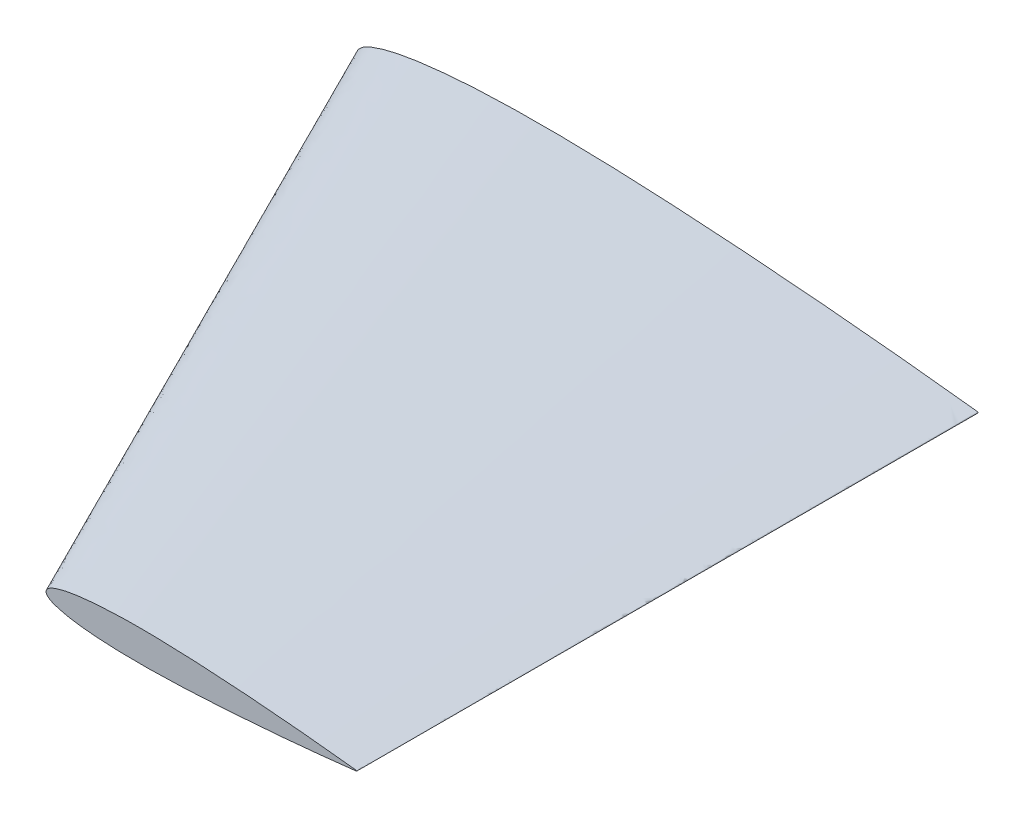
SolidWorks part; units mm, degrees
ref_plane "Front Plane" through (0, 0, 0) normal (0, 0, 1) x (1, 0, 0)
ref_plane "Top Plane" through (0, 0, 0) normal (0, 1, 0) x (1, 0, 0)
ref_plane "Right Plane" through (0, 0, 0) normal (1, 0, 0) x (0, 0, -1)
curve "Curve5"
  spline degree 3 poles (200, 0.21, 0) (196.6671, 0.5908, 0) (190.0035, 1.3521, 0) (176.6737, 2.7751, 0) (160.0099, 4.4044, 0) (140.0096, 6.1482, 0) (120.0099, 7.658, 0) (100.0092, 8.876, 0) (80.0082, 9.7553, 0) (63.3342, 10.0604, 0) (49.9974, 9.9402, 0) (39.9929, 9.6083, 0) (29.9799, 8.984, 0) (21.645, 8.086, 0) (14.9711, 7.038, 0) (9.9602, 5.9907, 0) (5.6938, 4.6887, 0) (2.1576, 3.1984, 0) (-1.278, 0, 0) (2.1576, -3.1984, 0) (5.6938, -4.6887, 0) (9.9602, -5.9907, 0) (14.9711, -7.038, 0) (21.645, -8.086, 0) (29.9799, -8.984, 0) (39.9929, -9.6083, 0) (49.9974, -9.9402, 0) (63.3342, -10.0604, 0) (80.0082, -9.7553, 0) (100.0092, -8.876, 0) (120.0099, -7.658, 0) (140.0096, -6.1482, 0) (160.0099, -4.4044, 0) (176.6737, -2.7751, 0) (190.0035, -1.3521, 0) (196.6671, -0.5908, 0) (200, -0.21, 0) knots 0 0 0 0 0.024822 0.049628 0.099196 0.148713 0.198182 0.247603 0.296978 0.346315 0.370982 0.395662 0.420379 0.445196 0.457685 0.470303 0.483222 0.490061 0.5 0.509939 0.516778 0.529697 0.542315 0.554804 0.579621 0.604338 0.629018 0.653685 0.703022 0.752397 0.801818 0.851287 0.900804 0.950372 0.975178 1 1 1 1
sketch "Sketch7" plane through (0, 0, 0) normal (0, 0, 1) x (1, 0, 0)
  arc A0 (200, 0.21) -> (200, -0.21) centre (199.976, 0) cw
  spline S0 degree 3 poles (945.0025, 1829.266) (549.2126, -75.4811) (368.3894, -17.6906) (176.6737, 2.7751) (160.0099, 4.4044) (140.0096, 6.1482) (120.0099, 7.658) (100.0092, 8.876) (80.0082, 9.7553) (63.3342, 10.0604) (49.9974, 9.9402) (39.9929, 9.6083) (29.9799, 8.984) (21.645, 8.086) (14.9711, 7.038) (9.9602, 5.9907) (5.6938, 4.6887) (2.1576, 3.1984) (-1.278, 0) (2.1576, -3.1984) (5.6938, -4.6887) (9.9602, -5.9907) (14.9711, -7.038) (21.645, -8.086) (29.9799, -8.984) (39.9929, -9.6083) (49.9974, -9.9402) (63.3342, -10.0604) (80.0082, -9.7553) (100.0092, -8.876) (120.0099, -7.658) (140.0096, -6.1482) (160.0099, -4.4044) (176.6737, -2.7751) (368.389, 17.6906) (549.212, 75.4809) (945.0005, -1829.256) knots -1.327474 -1.327474 -1.327474 -1.327474 0.024822 0.049628 0.099196 0.148713 0.198182 0.247603 0.296978 0.346315 0.370982 0.395662 0.420379 0.445196 0.457685 0.470303 0.483222 0.490061 0.5 0.509939 0.516778 0.529697 0.542315 0.554804 0.579621 0.604338 0.629018 0.653685 0.703022 0.752397 0.801818 0.851287 0.900804 0.950372 0.975178 2.327471 2.327471 2.327471 2.327471 only from (200, 0.21) to (200, -0.21) construction
  spline S1 degree 3 poles (200, 0.21) (196.6671, 0.5908) (190.0035, 1.3521) (176.6737, 2.7751) (160.0099, 4.4044) (140.0096, 6.1482) (120.0099, 7.658) (100.0092, 8.876) (80.0082, 9.7553) (63.3342, 10.0604) (49.9974, 9.9402) (39.9929, 9.6083) (29.9799, 8.984) (21.645, 8.086) (14.9711, 7.038) (9.9602, 5.9907) (5.6938, 4.6887) (2.1576, 3.1984) (-1.278, 0) (2.1576, -3.1984) (5.6938, -4.6887) (9.9602, -5.9907) (14.9711, -7.038) (21.645, -8.086) (29.9799, -8.984) (39.9929, -9.6083) (49.9974, -9.9402) (63.3342, -10.0604) (80.0082, -9.7553) (100.0092, -8.876) (120.0099, -7.658) (140.0096, -6.1482) (160.0099, -4.4044) (176.6737, -2.7751) (190.0035, -1.3521) (196.6671, -0.5908) (200, -0.21) knots 0 0 0 0 0.024822 0.049628 0.099196 0.148713 0.198182 0.247603 0.296978 0.346315 0.370982 0.395662 0.420379 0.445196 0.457685 0.470303 0.483222 0.490061 0.5 0.509939 0.516778 0.529697 0.542315 0.554804 0.579621 0.604338 0.629018 0.653685 0.703022 0.752397 0.801818 0.851287 0.900804 0.950372 0.975178 1 1 1 1
  point P3 (0, 0)
ref_plane "Plane3" through (0, 0, 0) normal (0, 0, 1) x (1, 0, 0)
ref_plane "Plane4" through (0, 0, 200) normal (0, 0, 1) x (1, 0, 0)
sketch "Sketch8" plane through (0, 0, 200) normal (0, 0, 1) x (1, 0, 0)
  arc A0 (199.988, -0.105) -> (199.988, 0.105) centre (199.976, 0) ccw
  spline S1 degree 3 poles (199.988, 0.105) (198.3216, 0.2954) (194.9898, 0.6761) (188.3248, 1.3875) (179.993, 2.2022) (169.9928, 3.0741) (159.9929, 3.829) (149.9926, 4.438) (139.9921, 4.8777) (131.6551, 5.0302) (124.9867, 4.9701) (119.9845, 4.8041) (114.978, 4.492) (110.8105, 4.043) (107.4736, 3.519) (104.9681, 2.9953) (102.8349, 2.3443) (101.0668, 1.5992) (99.349, 0) (101.0668, -1.5992) (102.8349, -2.3443) (104.9681, -2.9953) (107.4736, -3.519) (110.8105, -4.043) (114.978, -4.492) (119.9845, -4.8041) (124.9867, -4.9701) (131.6551, -5.0302) (139.9921, -4.8777) (149.9926, -4.438) (159.9929, -3.829) (169.9928, -3.0741) (179.993, -2.2022) (188.3248, -1.3875) (194.9898, -0.6761) (198.3216, -0.2954) (199.988, -0.105) knots 0 0 0 0 0.024822 0.049628 0.099196 0.148713 0.198182 0.247603 0.296978 0.346315 0.370982 0.395662 0.420379 0.445196 0.457685 0.470303 0.483222 0.490061 0.5 0.509939 0.516778 0.529697 0.542315 0.554804 0.579621 0.604338 0.629018 0.653685 0.703022 0.752397 0.801818 0.851287 0.900804 0.950372 0.975178 1 1 1 1
loft "Loft6" add profiles "Sketch7", "Sketch8"
